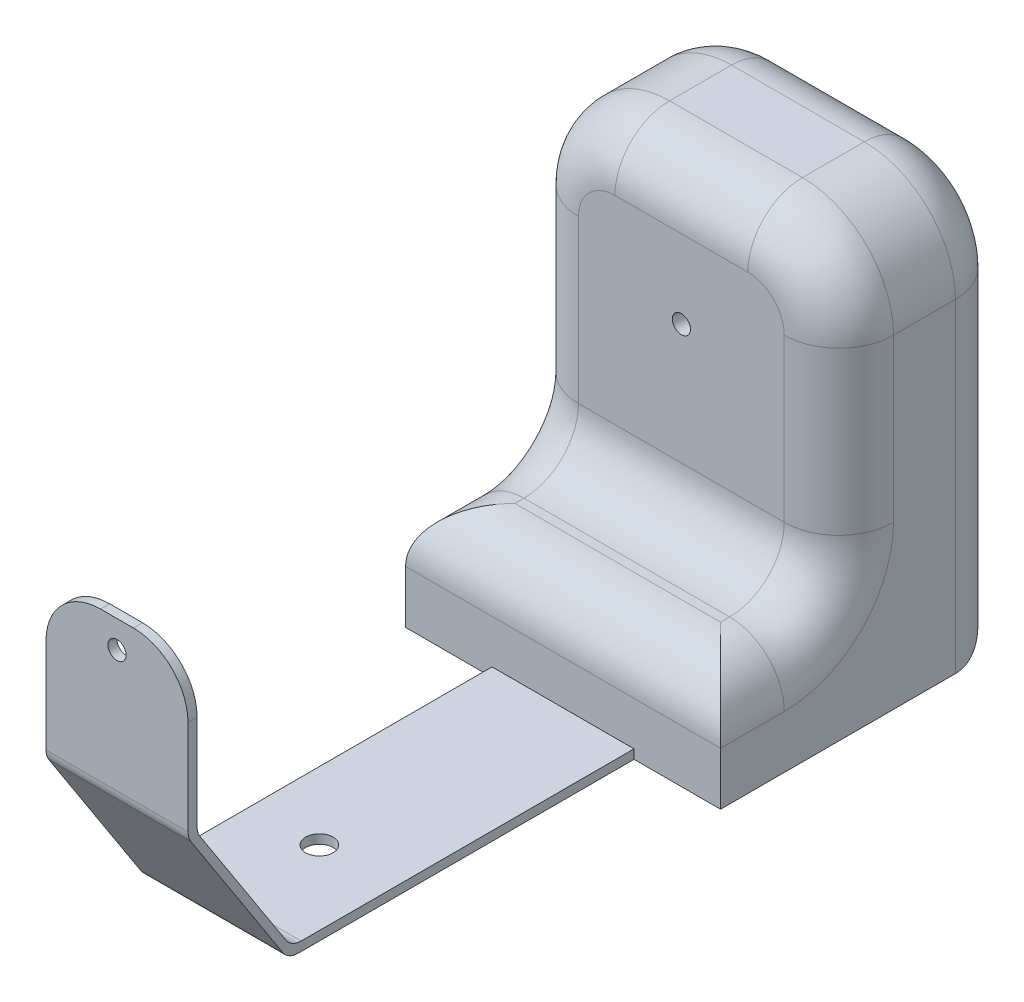
SolidWorks part; units mm, degrees
ref_plane "Front Plane" through (0, 0, 0) normal (0, 0, 1) x (1, 0, 0)
ref_plane "Top Plane" through (0, 0, 0) normal (0, 1, 0) x (1, 0, 0)
ref_plane "Right Plane" through (0, 0, 0) normal (1, 0, 0) x (0, 0, -1)
sketch "Sketch1" plane through (0, 0, 0) normal (1, 0, 0) x (0, 0, -1)
  line L0 (-38.8781, 93.7878) -> (-38.8781, 8.7878)
  line L1 (-38.8781, 8.7878) -> (16.1219, -76.2122)
  line L2 (16.1219, -76.2122) -> (361.1219, -76.2122)
  line L3 (361.1219, -76.2122) -> (361.1219, 123.7878)
  line L4 (-38.8781, 93.7878) -> (-33.8781, 93.7878)
  line L5 (-33.8781, 93.7878) -> (-33.8781, 8.7878)
  line L6 (-33.8781, 8.7878) -> (17.8866, -71.2122)
  line L7 (17.8866, -71.2122) -> (356.1219, -71.2122)
  line L8 (361.1219, 123.7878) -> (356.1219, 123.7878)
  line L9 (356.1219, 123.7878) -> (356.1219, -71.2122)
  dimension "D1" = 85
  dimension "D2" = 55
  dimension "D3" = 85
  dimension "D4" = 345
  dimension "D5" = 200
  dimension "D6" = 5
  dimension "D7" = 5
  dimension "D8" = 5
extrude "Extrude1" add sketch "Sketch1" along normal blind 78
fillet "Fillet1" radius 20 2 edges at (39, -76.2122, -361.1219) (39, -71.2122, -356.1219)
fillet "Fillet2" radius 10 4 edges at (39, 8.7878, 38.8781) (39, 8.7878, 33.8781) (39, -71.2122, -17.8866) (39, -76.2122, -16.1219)
sketch "Sketch3" plane through (0, -71.2122, 0) normal (0, 1, 0) x (1, 0, 0)
  line L0 (0, 23.3269) -> (78, 23.3269) construction
  line L1 (78, 361.1219) -> (0, 361.1219) construction
  circle A0 centre (37.2763, 74.0019) radius 7.5
  dimension "D1" = 15
  dimension "D2" = 50.675
  dimension "D3" = 287.12
extrude "Extrude3" cut sketch "Sketch3" against normal through all
fillet "Fillet3" radius 30 2 edges at (0, 93.7878, 36.3781) (78, 93.7878, 36.3781)
sketch "Sketch4" plane through (78, 0, 0) normal (1, 0, 0) x (0, 0, -1)
  line L0 (-38.8781, 63.7878) -> (-38.8781, 11.7409) construction
  line L1 (206.1219, 176.4782) -> (482.7611, 176.4782)
  line L2 (206.1219, 176.4782) -> (206.1219, -134.0922)
  line L3 (206.1219, -134.0922) -> (482.7611, -134.0922)
  line L4 (482.7611, 176.4782) -> (482.7611, -134.0922)
  dimension "D1" = 245
extrude "Extrude4" cut sketch "Sketch4" against normal through all
sketch "Sketch5" plane through (0, 0, -206.1219) normal (0, 0, -1) x (-1, 0, 0)
  line L0 (-78, -66.6448) -> (-78, 6.3084) construction
  line L1 (-125.5, -76.2122) -> (47.5, -76.2122)
  line L2 (-125.5, -76.2122) -> (-125.5, -17.2122)
  line L3 (-125.5, -17.2122) -> (47.5, -17.2122)
  line L4 (47.5, -76.2122) -> (47.5, -17.2122)
  line L5 (0, -66.6448) -> (0, 6.3084) construction
  line L6 (0, -76.2122) -> (-78, -76.2122) construction
  dimension "D1" = 173
  dimension "D2" = 47.5
  dimension "D3" = 47.5
  dimension "D4" = 59
  dimension "D5" = 59
extrude "Extrude5" add sketch "Sketch5" along normal blind 65
sketch "Sketch6" plane through (0, 0, -271.1219) normal (0, 0, -1) x (-1, 0, 0)
  line L1 (-125.5, -76.2122) -> (47.5, -76.2122)
  line L2 (-125.5, -76.2122) -> (-125.5, 101.7878)
  line L3 (-75.5, 151.7878) -> (-2.5, 151.7878)
  line L4 (47.5, -76.2122) -> (47.5, 101.7878)
  arc A0 (-2.5, 151.7878) -> (47.5, 101.7878) centre (-2.5, 101.7878) cw
  arc A1 (-75.5, 151.7878) -> (-125.5, 101.7878) centre (-75.5, 101.7878) ccw
  point P8 (47.5, 151.7878)
  point P11 (-125.5, 151.7878)
  dimension "D3" = 50
  dimension "D1" = 173
  dimension "D2" = 228
extrude "Extrude6" add sketch "Sketch6" along normal blind 94
sketch "Sketch2" plane through (0, 0, 38.8781) normal (0, 0, 1) x (1, 0, 0)
  line L0 (48, 93.7878) -> (30, 93.7878) construction
  line L1 (0, 63.7878) -> (0, 11.7409) construction
  circle A0 centre (39, 78.7878) radius 5
  dimension "D1" = 10
  dimension "D2" = 15
  dimension "D3" = 39
extrude "Extrude2" cut sketch "Sketch2" against normal through all
fillet "Fillet4" radius 30 9 edges at (-32.8553, 137.1431, -271.1219) (110.8553, 137.1431, -271.1219) (39, 151.7878, -271.1219) (39, -17.2122, -206.1219)
fillet "Fillet5" radius 30 6 edges at (-47.5, 12.7878, -365.1219) (-32.8553, 137.1431, -365.1219) (39, 151.7878, -365.1219) (110.8553, 137.1431, -365.1219) (39, -76.2122, -365.1219) (125.5, 12.7878, -365.1219)
